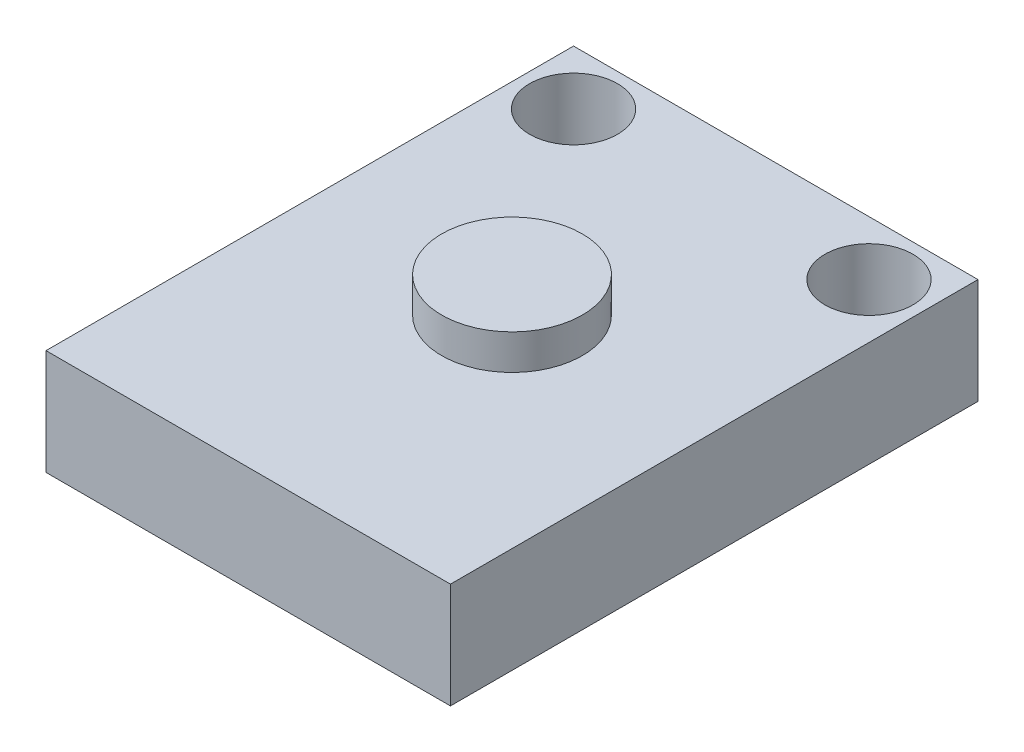
SolidWorks part; units mm, degrees
ref_plane "Front Plane" through (0, 0, 0) normal (0, 0, 1) x (1, 0, 0)
ref_plane "Top Plane" through (0, 0, 0) normal (0, 1, 0) x (1, 0, 0)
ref_plane "Right Plane" through (0, 0, 0) normal (1, 0, 0) x (0, 0, -1)
sketch "Sketch1" plane through (0, 0, 0) normal (0, 1, 0) x (1, 0, 0)
  line L0 (11.5, 11.9) -> (10.9, 11.9) construction
  line L1 (-11.5, -15) -> (11.5, -15)
  line L2 (-11.5, -15) -> (-11.5, 15)
  line L3 (-11.5, 15) -> (11.5, 15)
  line L4 (11.5, -15) -> (11.5, 15)
  line L5 (-11.5, -15) -> (11.5, 15) construction
  line L6 (-11.5, 15) -> (11.5, -15) construction
  line L7 (8.4, 14.4) -> (8.4, 15) construction
  line L9 (-10.9, 11.9) -> (-11.5, 11.9) construction
  circle A0 centre (-8.4, 11.9) radius 2.5
  circle A1 centre (8.4, 11.9) radius 2.5
  point P0 (0, 0)
  dimension "D3" = 5
  dimension "D1" = 23
  dimension "D2" = 30
  dimension "D4" = 0.6
  dimension "D5" = 0.6
  dimension "D6" = 0.6
extrude "Boss-Extrude1" add sketch "Sketch1" along normal blind 6
sketch "Sketch2" plane through (0, 6, 0) normal (0, 1, 0) x (1, 0, 0)
  circle A0 centre (0, 0) radius 4
  dimension "D1" = 8
extrude "Boss-Extrude2" add sketch "Sketch2" along normal blind 8 from surface at -6 starting at face at (-8.4, 0, -9.4)
